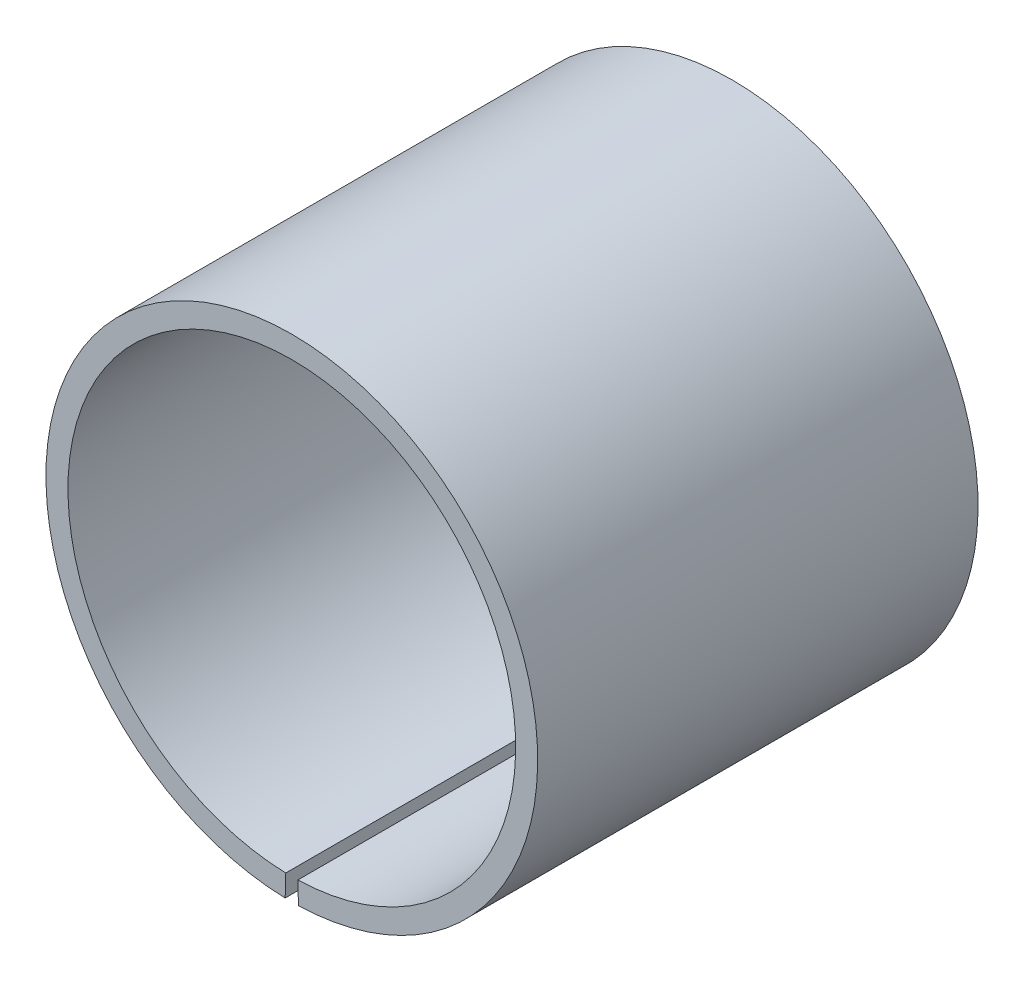
SolidWorks part; units mm, degrees
ref_plane "Front Plane" through (0, 0, 0) normal (0, 0, 1) x (1, 0, 0)
ref_plane "Top Plane" through (0, 0, 0) normal (0, 1, 0) x (1, 0, 0)
ref_plane "Right Plane" through (0, 0, 0) normal (1, 0, 0) x (0, 0, -1)
sketch "Sketch1" plane through (0, 0, 0) normal (0, 0, 1) x (1, 0, 0)
  line L1 (-0.4118, -15.2444) -> (-0.4523, -16.7439)
  line L3 (0.4523, -16.7439) -> (0.4118, -15.2444)
  arc A0 (0.4118, -15.2444) -> (-0.4118, -15.2444) centre (0, 0) ccw
  arc A1 (0.4523, -16.7439) -> (-0.4523, -16.7439) centre (0, 0) ccw
  dimension "D1" = 1.5
  dimension "D2" = 30.5
extrude "Boss-Extrude1" add sketch "Sketch1" along normal mid plane 30
